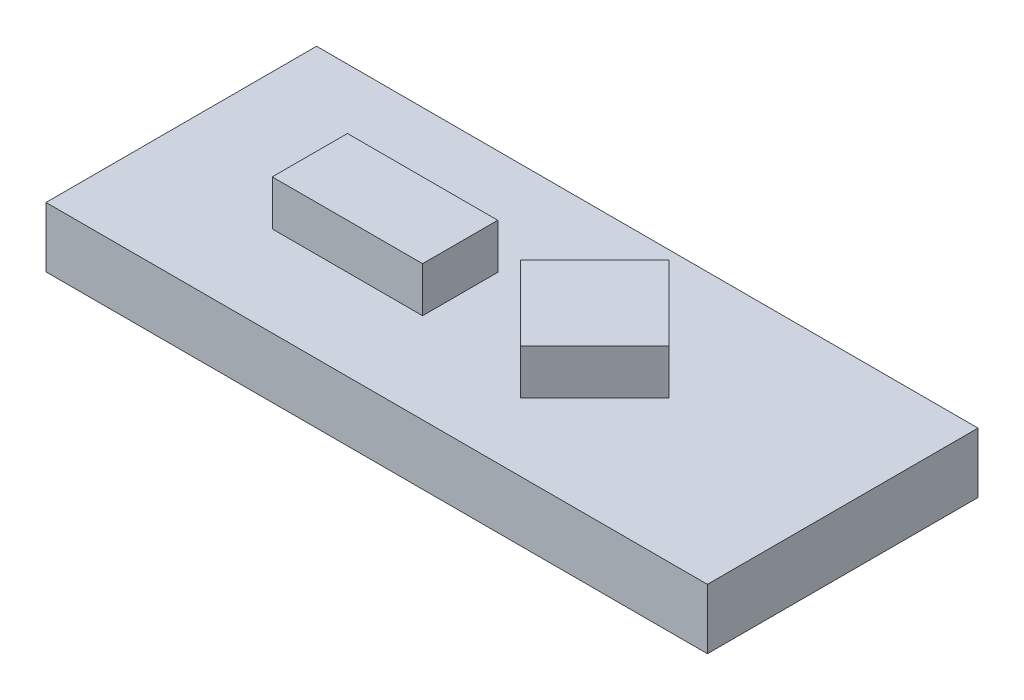
SolidWorks part; units mm, degrees
ref_plane "Front Plane" through (0, 0, 0) normal (0, 0, 1) x (1, 0, 0)
ref_plane "Top Plane" through (0, 0, 0) normal (0, 1, 0) x (1, 0, 0)
ref_plane "Right Plane" through (0, 0, 0) normal (1, 0, 0) x (0, 0, -1)
sketch "Sketch1" plane through (0, 0, 0) normal (0, 1, 0) x (1, 0, 0)
  line L1 (-23.9263, 12.8756) -> (20.0737, 12.8756)
  line L2 (-23.9263, 12.8756) -> (-23.9263, -5.1244)
  line L3 (-23.9263, -5.1244) -> (20.0737, -5.1244)
  line L4 (20.0737, 12.8756) -> (20.0737, -5.1244)
  dimension "D1" = 44
  dimension "D2" = 18
extrude "Boss-Extrude1" add sketch "Sketch1" along normal blind 4
sketch "Sketch2" plane through (0, 4, 0) normal (0, 1, 0) x (1, 0, 0)
  line L0 (-23.9263, -5.1244) -> (20.0737, -5.1244) construction
  line L1 (-14.8737, 5.8756) -> (-4.8737, 5.8756)
  line L2 (-14.8737, 5.8756) -> (-14.8737, 0.8756)
  line L3 (-14.8737, 0.8756) -> (-4.8737, 0.8756)
  line L4 (-4.8737, 5.8756) -> (-4.8737, 0.8756)
  line L5 (-1.8258, 4.3253) -> (3.124, -0.6244)
  line L6 (-1.8258, 4.3253) -> (3.124, 9.2751)
  line L7 (3.124, -0.6244) -> (8.0737, 4.3253)
  line L8 (3.124, 9.2751) -> (8.0737, 4.3253)
  line L9 (20.0737, -5.1244) -> (20.0737, 12.8756) construction
  line L10 (20.0737, 12.8756) -> (-23.9263, 12.8756) construction
  dimension "D1" = 6
  dimension "D2" = 5
  dimension "D3" = 10
  dimension "D4" = 7
  dimension "D5" = 7
  dimension "D6" = 12
  dimension "D7" = 4.5
  dimension "D8" = 3.6005
extrude "Boss-Extrude2" add sketch "Sketch2" along normal blind 3
